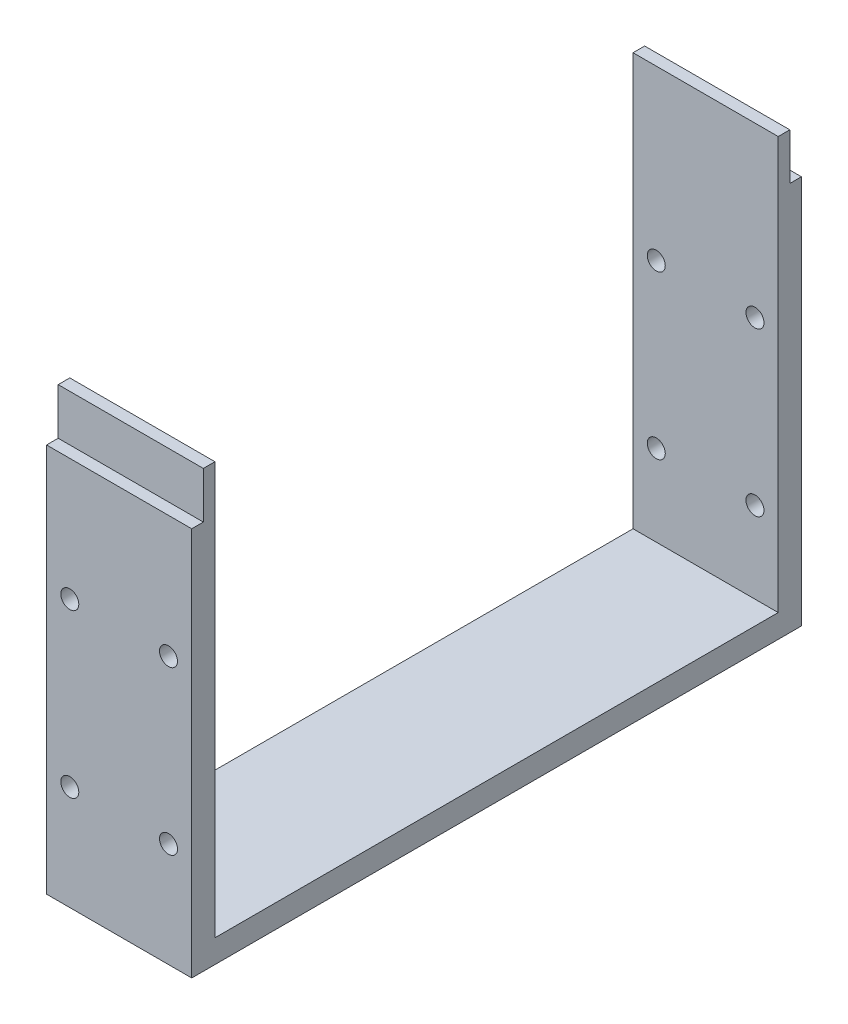
SolidWorks part; units mm, degrees
ref_plane "Front Plane" through (0, 0, 0) normal (0, 0, 1) x (1, 0, 0)
ref_plane "Top Plane" through (0, 0, 0) normal (0, 1, 0) x (1, 0, 0)
ref_plane "Right Plane" through (0, 0, 0) normal (1, 0, 0) x (0, 0, -1)
sketch "Sketch1" plane through (0, 0, 0) normal (1, 0, 0) x (0, 0, -1)
  line L1 (-52.5, 2) -> (52.5, 2)
  line L2 (-52.5, 2) -> (-52.5, -2)
  line L3 (-52.5, -2) -> (52.5, -2)
  line L4 (52.5, 2) -> (52.5, -2)
  line L5 (-52.5, 2) -> (52.5, -2) construction
  line L6 (-52.5, -2) -> (52.5, 2) construction
  line L7 (-52.5, 2) -> (-48.5, 2)
  line L8 (-52.5, 2) -> (-52.5, 65)
  line L9 (-52.5, 65) -> (-48.5, 65)
  line L10 (-48.5, 2) -> (-48.5, 65)
  line L11 (-48.5, 65) -> (-50.5, 65)
  line L12 (-48.5, 65) -> (-48.5, 73)
  line L13 (-48.5, 73) -> (-50.5, 73)
  line L14 (-50.5, 65) -> (-50.5, 73)
  line L15 (52.5, 2) -> (48.5, 2)
  line L16 (52.5, 2) -> (52.5, 65)
  line L17 (52.5, 65) -> (48.5, 65)
  line L18 (48.5, 2) -> (48.5, 65)
  line L19 (48.5, 65) -> (50.5, 65)
  line L20 (48.5, 65) -> (48.5, 73)
  line L21 (48.5, 73) -> (50.5, 73)
  line L22 (50.5, 65) -> (50.5, 73)
  point P0 (0, 0)
  dimension "D1" = 105
  dimension "D2" = 4
  dimension "D3" = 4
  dimension "D4" = 63
  dimension "D5" = 8
  dimension "D6" = 2
  dimension "D7" = 4
  dimension "D8" = 63
  dimension "D9" = 2
  dimension "D10" = 8
extrude "Boss-Extrude1" add sketch "Sketch1" along normal mid plane 25 contours L4 L1 L2 L3 | L1 L10 L9 L8 | L18 L1 L16 L17 | L12 L11 L14 L13 | L20 L19 L22 L21
sketch "Sketch2" plane through (0, 0, 48.5) normal (0, 0, -1) x (-1, 0, 0)
  line L0 (-12.5, 2) -> (-12.5, 73) construction
  line L1 (-12.5, 2) -> (12.5, 2) construction
  line L2 (0, 73) -> (0, 7.1275) construction
  line L3 (-12.5, 73) -> (12.5, 73) construction
  circle A0 centre (-8.5, 16) radius 1.55
  circle A1 centre (-8.5, 44) radius 1.55
  circle A2 centre (8.5, 16) radius 1.55
  circle A3 centre (8.5, 44) radius 1.55
  dimension "D1" = 3.1
  dimension "D2" = 4
  dimension "D3" = 14
  dimension "D4" = 3.1
  dimension "D5" = 28
extrude "Cut-Extrude2" cut sketch "Sketch2" against normal through all both and the other way through all
